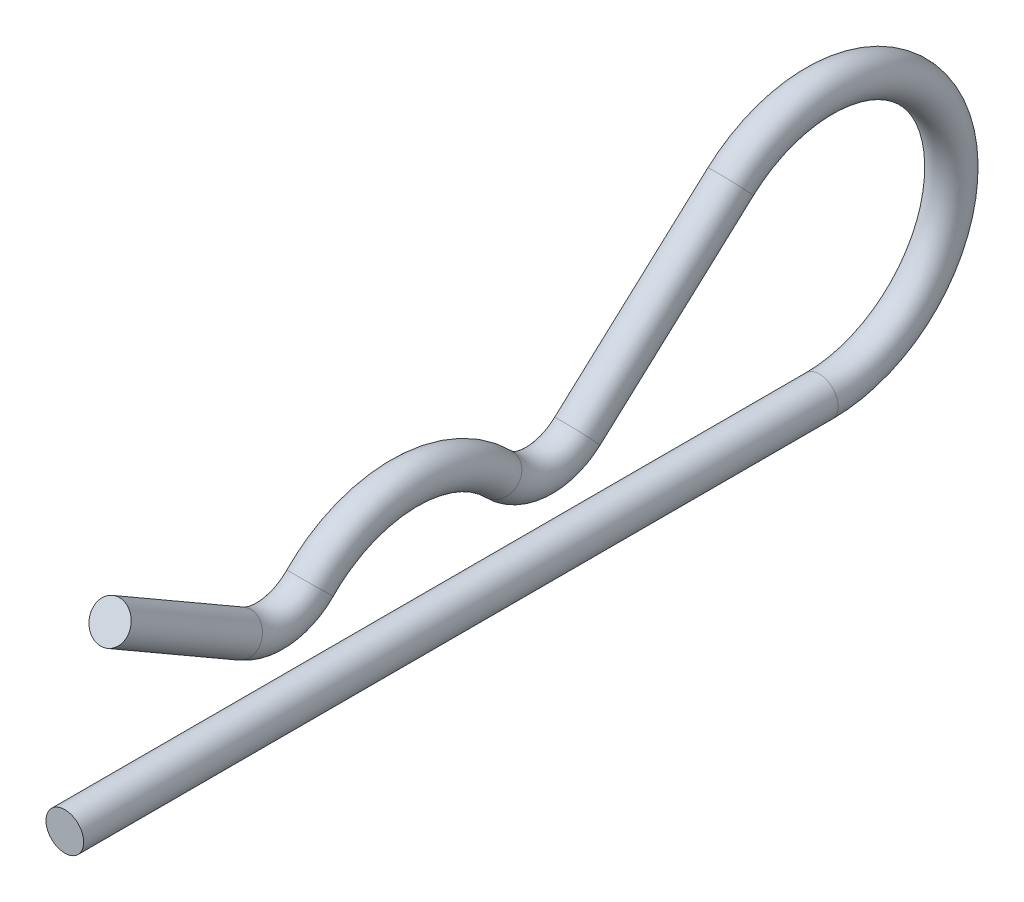
SolidWorks part; units mm, degrees
ref_plane "Front" through (0, 0, 0) normal (0, 0, 1) x (1, 0, 0)
ref_plane "Top" through (0, 0, 0) normal (0, 1, 0) x (1, 0, 0)
ref_plane "Right" through (0, 0, 0) normal (1, 0, 0) x (0, 0, -1)
sketch "Sketch1" plane through (0, 0, 0) normal (1, 0, 0) x (0, 0, -1)
  line L0 (-36, 0) -> (24, 0) construction
  line L1 (-19.7121, 10.5) -> (1.7121, 10.5) construction
  line L2 (36, 0) -> (36, 10.5) construction
  line L3 (36, 10.5) -> (34.5, 10.5) construction
  line L4 (-36, 0) -> (-36, 1.5) construction
  line L5 (36, 0) -> (-36, 0) construction
  line L6 (-21.9621, 6.6029) -> (-32.4, 12.6292) construction
  line L7 (-9, 10.5) -> (-9, 0) construction
  line L8 (-36, 0) -> (-36, -1.5) construction
  line L13 (16.9334, 18.2661) -> (4.7407, 7.1717) construction
  circle A0 centre (24, 10.5) radius 9 construction
  arc A1 (-1.5015, 7.35) -> (-16.4985, 7.35) centre (-9, 0) ccw construction
  arc A6 (-16.4985, 7.35) -> (-21.9621, 6.6029) centre (-19.7121, 10.5) cw construction
  arc A8 (4.7407, 7.1717) -> (-1.5015, 7.35) centre (1.7121, 10.5) cw construction
  arc A9 (24, 0) -> (16.9334, 18.2661) centre (24, 10.5) ccw construction
  point P2 (0, 0)
  dimension "D1" = 4.5
  dimension "D2" = 27
  dimension "D5" = 3.6
  dimension "D9" = 30
  dimension "D11" = 1.5
  dimension "D3" = 1.5
  dimension "Wire OD" = 3
ref_plane "Plane1" through (0, 0, 36) normal (0, 0, 1) x (1, 0, 0)
sketch "Sketch2" plane through (0, 0, 36) normal (0, 0, 1) x (1, 0, 0)
  circle A0 centre (0, 0) radius 1.5
sketch "Sketch3" plane through (0, 0, 0) normal (1, 0, 0) x (0, 0, -1)
  line L0 (-21.9621, 6.6029) -> (-32.4, 12.6292) construction
  line L1 (16.9334, 18.2661) -> (4.7407, 7.1717) construction
  line L2 (-36, 0) -> (24, 0) construction
  line L3 (-21.9621, 6.6029) -> (-32.4, 12.6292)
  line L4 (16.9334, 18.2661) -> (4.7407, 7.1717)
  line L5 (-36, 0) -> (24, 0)
  arc A0 (-21.9621, 6.6029) -> (-16.4985, 7.35) centre (-19.7121, 10.5) ccw construction
  arc A1 (-1.5015, 7.35) -> (-16.4985, 7.35) centre (-9, 0) ccw construction
  arc A2 (-1.5015, 7.35) -> (4.7407, 7.1717) centre (1.7121, 10.5) ccw construction
  arc A3 (24, 0) -> (16.9334, 18.2661) centre (24, 10.5) ccw construction
  arc A4 (-21.9621, 6.6029) -> (-16.4985, 7.35) centre (-19.7121, 10.5) ccw
  arc A5 (-1.5015, 7.35) -> (-16.4985, 7.35) centre (-9, 0) ccw
  arc A6 (-1.5015, 7.35) -> (4.7407, 7.1717) centre (1.7121, 10.5) ccw
  arc A7 (24, 0) -> (16.9334, 18.2661) centre (24, 10.5) ccw
sweep "Sweep1" add profiles "Sketch2" path "Sketch3"
equation "\"D11@Sketch1\" = \"Wire OD@Sketch1\" / 2"
equation "\"D1@Sketch1\" = \"EyeID@Sketch1\" / 4"
equation "\"D3@Sketch1\" = \"D11@Sketch1\""
equation "\"D2@Sketch1\" =  ( \"Length@Sketch1\" - \"EyeID@Sketch1\" )  / 2"
equation "\"D5@Sketch1\" = \"Length@Sketch1\" * .05"
